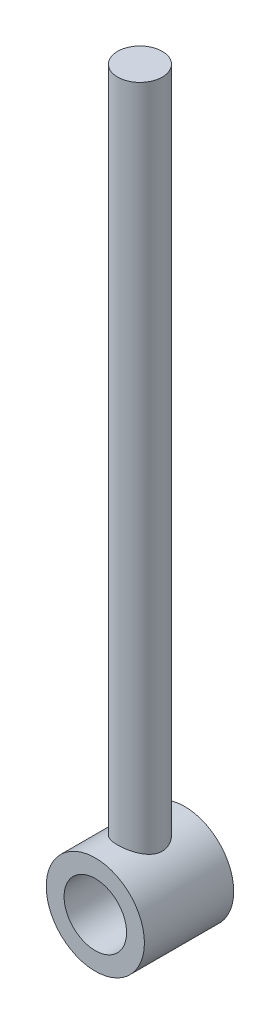
SolidWorks part; units mm, degrees
ref_plane "Front Plane" through (0, 0, 0) normal (0, 0, 1) x (1, 0, 0)
ref_plane "Top Plane" through (0, 0, 0) normal (0, 1, 0) x (1, 0, 0)
ref_plane "Right Plane" through (0, 0, 0) normal (1, 0, 0) x (0, 0, -1)
sketch "Sketch1" plane through (0, 0, 0) normal (0, 0, 1) x (1, 0, 0)
  circle A0 centre (0, 0) radius 3.5
  circle A1 centre (0, 0) radius 5.5
  dimension "D1" = 7
  dimension "D2" = 11
extrude "Boss-Extrude1" add sketch "Sketch1" along normal blind 10
sketch "Sketch2" plane through (0, 0, 0) normal (0, 1, 0) x (1, 0, 0)
  line L0 (5.5, 0) -> (-5.5, 0) construction
  circle A0 centre (0, -5) radius 2.5
  dimension "D2" = 5
  dimension "D1" = 5
extrude "Boss-Extrude2" add sketch "Sketch2" along normal blind 80
sketch "Sketch3" plane through (0, 0, 10) normal (0, 0, 1) x (1, 0, 0)
  circle A0 centre (0, 0) radius 3.5
extrude "Cut-Extrude1" cut sketch "Sketch3" against normal through all
